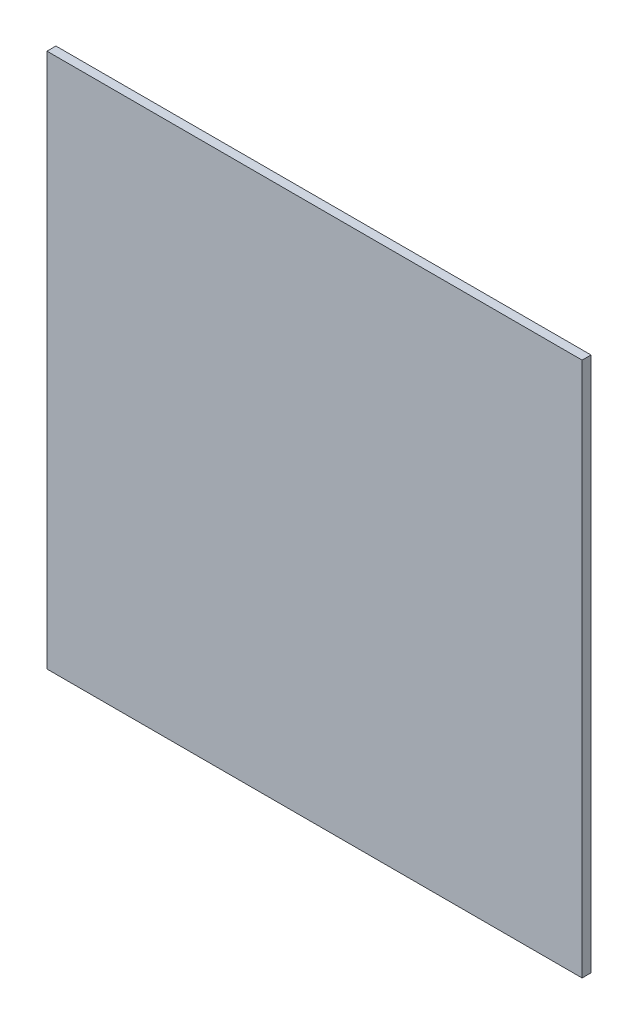
SolidWorks part; units mm, degrees
ref_plane "Płaszczyzna przednia" through (0, 0, 0) normal (0, 0, 1) x (1, 0, 0)
ref_plane "Płaszczyzna górna" through (0, 0, 0) normal (0, 1, 0) x (1, 0, 0)
ref_plane "Płaszczyzna prawa" through (0, 0, 0) normal (1, 0, 0) x (0, 0, -1)
sketch "Szkic1" plane through (0, 0, 0) normal (0, 0, 1) x (1, 0, 0)
  line L1 (0, 0) -> (300, 0)
  line L2 (0, 0) -> (0, 300)
  line L3 (0, 300) -> (300, 300)
  line L4 (300, 0) -> (300, 300)
  dimension "D1" = 300
  dimension "D2" = 300
extrude "Dodanie-wyciągnięcie1" add sketch "Szkic1" along normal blind 5
